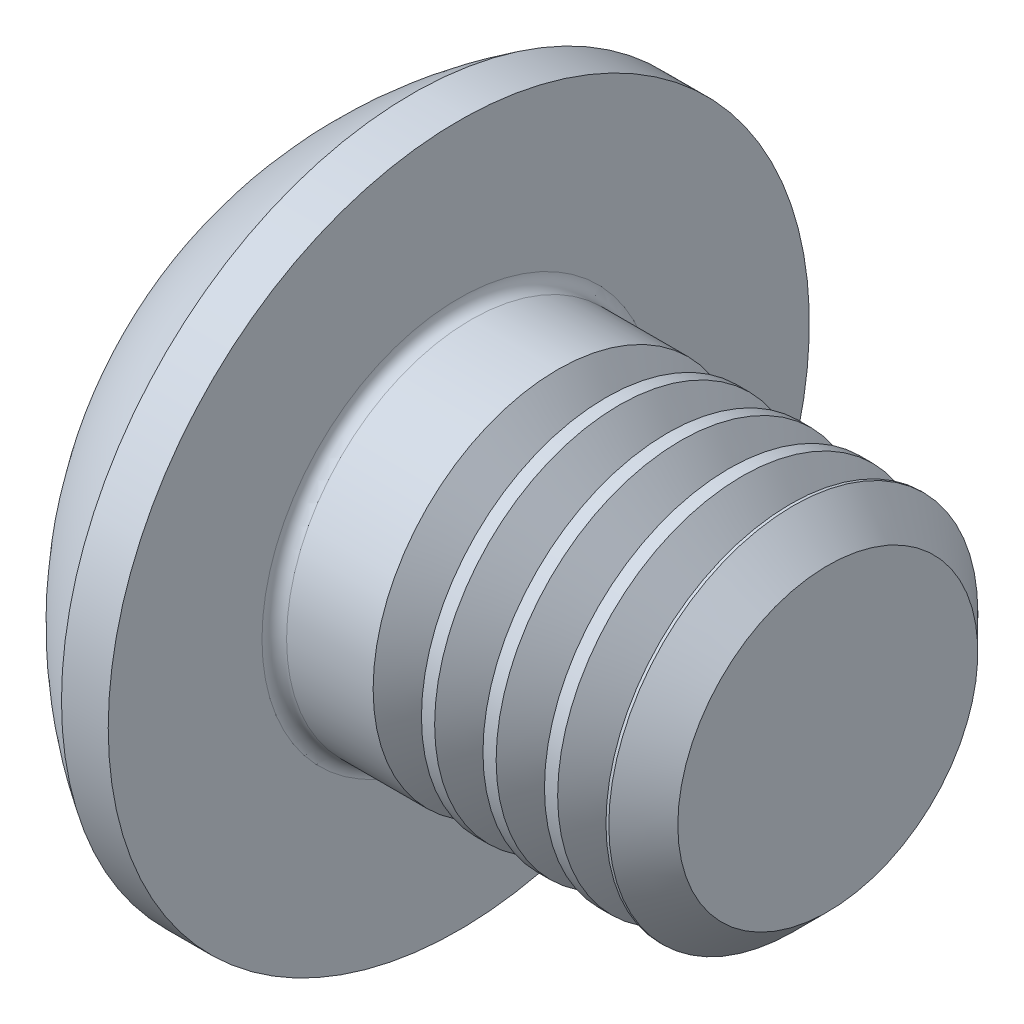
SolidWorks part; units mm, degrees
ref_plane "Plane1" through (0, 0, 0) normal (0, 0, 1) x (1, 0, 0)
ref_plane "Plane2" through (0, 0, 0) normal (0, 1, 0) x (1, 0, 0)
ref_plane "Plane3" through (0, 0, 0) normal (1, 0, 0) x (0, 0, -1)
sketch "BodySke" plane through (0, 0, 0) normal (0, 0, 1) x (1, 0, 0)
  line L0 (4.65, 0) -> (4.65, 1.2195)
  line L1 (4.3695, 1.5) -> (1.65, 1.5)
  line L2 (1.65, 1.5) -> (1.65, 2.85)
  line L3 (1.65, 2.85) -> (1.27, 2.85)
  line L4 (0, 0) -> (101.6, 0) construction
  line L5 (1.65, -2.85) -> (1.27, -2.85) construction
  line L6 (55.6768, -1.5) -> (1.65, -1.5) construction
  line L7 (4.65, 0) -> (0, 0)
  line L8 (0, 1.425) -> (0, -1.425) construction
  line L9 (0, 0) -> (0, 1.425)
  line L10 (4.65, 1.2195) -> (4.3695, 1.5)
  line L11 (4.65, -1.2195) -> (4.3695, -1.5) construction
  line L12 (2.15, 9.525) -> (2.15, -1.5) construction
  line L13 (1.65, 9.525) -> (1.65, -1.5) construction
  arc A1 (0, 1.425) -> (1.27, 2.85) centre (3.0334, 0) cw
  dimension "Diameter" = 3
  dimension "Length" = 3
  dimension "Head_dia" = 5.7
  dimension "D1" = 2.85
  dimension "Head_ht" = 1.65
  dimension "Head_side_ht" = 0.38
  dimension "Minor_dia" = 2.439
  dimension "Body_ch_ang" = 45
  dimension "Advance" = 0.5
  dimension "Thread_nom" = 3
revolve "BaseBody" add sketch "BodySke" angle 360 about L4
cosmetic thread "ThreadCosmetic" [suppressed] parameters "Thread_length"=2, "Thread_minor"=2.439
fillet "Fillet1" radius 0.1 1 edges at (1.65, 0, 1.5)
sketch "Sketch2" plane through (0, 0, 0) normal (0, 0, 1) x (1, 0, 0)
  line L0 (0, 1) -> (1.04, 1)
  line L1 (1.04, 1) -> (1.6174, 0)
  line L3 (1.6174, 0) -> (0, 0)
  line L4 (0, 0) -> (0, 1)
  line L5 (0, -1) -> (1.04, -1) construction
  line L6 (0, 0) -> (47.625, 0) construction
  dimension "D2" = 60
  dimension "PreBroach_depth" = 1.04
  dimension "PreBroach_dia" = 2
revolve "PreBroach" cut sketch "Sketch2" angle 360 about L6
sketch "Sketch3" plane through (0, 0, 0) normal (1, 0, 0) x (0, 0, -1)
  line L0 (-1, -0.5774) -> (-1, 0.5774)
  line L1 (-1, 0.5774) -> (0, 1.1547)
  line L2 (0, 1.1547) -> (1, 0.5774)
  line L3 (1, 0.5774) -> (1, -0.5774)
  line L4 (1, -0.5774) -> (0, -1.1547)
  line L5 (0, -1.1547) -> (-1, -0.5774)
  dimension "Hex_size" = 2
  dimension "D3" = 2
  dimension "D1" = 1
  dimension "D2" = 1
extrude "Hex" cut sketch "Sketch3" along normal blind 1.04
sketch "ThdSchSke" plane through (0, 0, 0) normal (0, 0, 1) x (1, 0, 0)
  line L0 (2.65, -1.2195) -> (2.4536, -1.5)
  line L1 (2.65, -1.2195) -> (2.8464, -1.5)
  line L2 (2.8464, -1.5) -> (2.8464, -1.875)
  line L3 (-3.175, 0) -> (5.1513, 0) construction
  line L5 (2.8464, -1.875) -> (2.4536, -1.875)
  line L6 (2.4536, -1.875) -> (2.4536, -1.5)
  dimension "Diameter" = 3
  dimension "Thread_minor" = 2.439
  dimension "SideAngle" = 55
  dimension "VeeAngle" = 70
  dimension "Overcut" = 3.75
  dimension "Start" = 2.65
revolve "ThreadSchematic" cut sketch "ThdSchSke" angle 360 about L3
pattern_linear "ThdSchPat" count 4 spacing 0.5 along (1, 0, 0) of "ThreadSchematic"
equation "\"D1@BodySke\" = \"Head_dia@BodySke\" * .5"
equation "\"Thread_minor@ThreadCosmetic\" = \"Minor_dia@BodySke\""
equation "\"D1@Sketch3\" = \"Hex_size@Sketch3\" / 2"
equation "\"D2@Sketch3\" = \"D1@Sketch3\""
equation "\"D3@Sketch3\" = \"Hex_size@Sketch3\""
equation "\"Thread_length@ThreadCosmetic\" = ((sgn( (\"Length@BodySke\" - \"Advance@BodySke\" * 2.0) - \"Thread_nom@BodySke\" )-1)*( (\"Length@BodySke\" - \"Advance@BodySke\" * 2.0) - \"Thread_nom@BodySke\" ))/-2+ \"Thread_nom@BodySke\""
equation "\"Thread_minor@ThdSchSke\" = \"Minor_dia@BodySke\""
equation "\"Diameter@ThdSchSke\" = \"Diameter@BodySke\""
equation "\"Overcut@ThdSchSke\" = \"Diameter@BodySke\" * 1.25"
equation "\"Start@ThdSchSke\" = \"Head_ht@BodySke\" + \"Length@BodySke\" - \"Thread_length@ThreadCosmetic\"  '---Non-countersunk---"
equation "\"Num_threads@ThdSchPat\" = int( \"Thread_length@ThreadCosmetic\" / \"Advance@BodySke\" + 0.999 )  + 1"
equation "\"Advance@ThdSchPat\" = \"Thread_length@ThreadCosmetic\" /  (\"Num_threads@ThdSchPat\" - 1) 'relax it"
equation "\"Num_threads@ThdSchPat\" = \"Num_threads@ThdSchPat\" - sgn( \"Num_threads@ThdSchPat\" - 1) '---chamfered tips only---"
